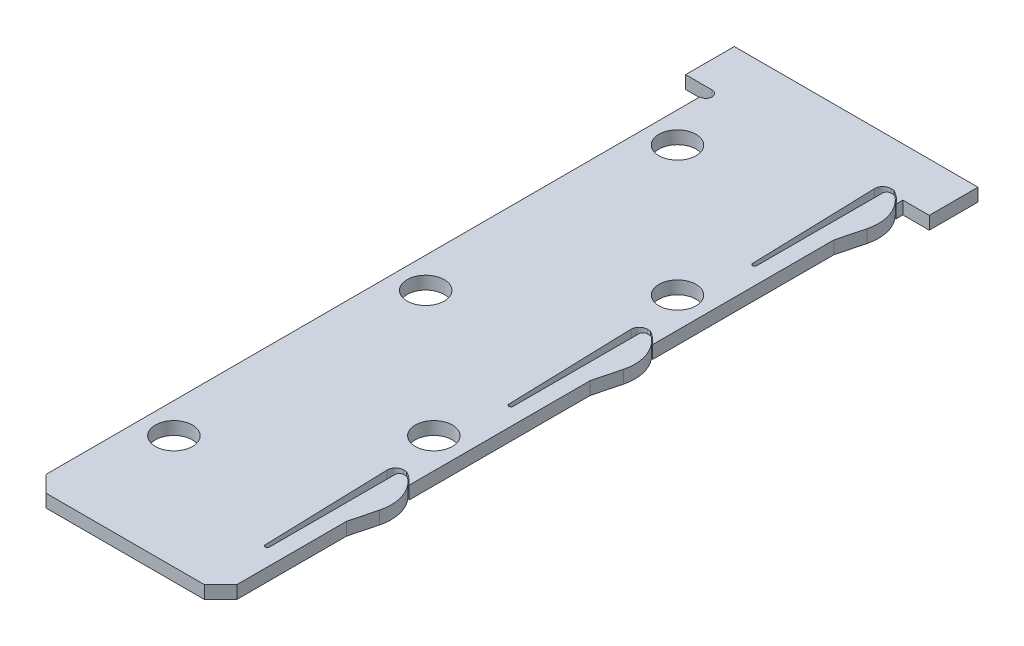
SolidWorks part; units mm, degrees
ref_plane "Front Plane" through (0, 0, 0) normal (0, 0, 1) x (1, 0, 0)
ref_plane "Top Plane" through (0, 0, 0) normal (0, 1, 0) x (1, 0, 0)
ref_plane "Right Plane" through (0, 0, 0) normal (1, 0, 0) x (0, 0, -1)
sketch "Sketch1" plane through (0, 0, 0) normal (0, 1, 0) x (1, 0, 0)
  line L0 (-11.75, -45) -> (11.75, 45) construction
  line L1 (-11.75, 45) -> (11.75, 45)
  line L2 (-11.75, 45) -> (-11.75, -45)
  line L3 (-11.75, -45) -> (11.75, -45)
  line L4 (11.75, 45) -> (11.75, -45)
  dimension "D1" = 23.5
  dimension "D2" = 90
extrude "Boss-Extrude1" add sketch "Sketch1" along normal blind 1.5875
sketch "Sketch2" plane through (0, 1.5875, 0) normal (0, 1, 0) x (1, 0, 0)
  line L0 (11.75, -45) -> (11.75, 45) construction
  line L1 (11.75, -29.5) -> (12.5905, -26.2529)
  line L2 (11.75, -29.5) -> (9.9294, -29.5)
  arc A0 (12.5905, -26.2529) -> (9.9294, -29.5) centre (7.75, -25) ccw
  dimension "D1" = 10
  dimension "D2" = 4
  dimension "D3" = 25
  dimension "D4" = 4.5
extrude "Boss-Extrude2" add sketch "Sketch2" against normal up to surface (1.5875 mm away) up to face at (0, 0, 0)
sketch "Sketch4" plane through (0, 1.5875, 0) normal (0, 1, 0) x (1, 0, 0)
  line L0 (10.75, -21) -> (9.75, -21)
  line L1 (9.75, -21) -> (9.75, -37)
  line L2 (9.2501, -37.0076) -> (8.75, -20.5)
  line L3 (8.75, -20.5) -> (10.15, -20.5)
  line L4 (11.75, -22) -> (11.75, 45) construction
  line L5 (11.75, -45) -> (11.75, -29.5) construction
  line L7 (11.75, -22) -> (11.75, -21.8361)
  arc A0 (11.75, -22) -> (10.75, -21) centre (7.75, -25) ccw
  arc A1 (12.5905, -26.2529) -> (11.75, -22) centre (7.75, -25) ccw construction
  arc A2 (10.15, -20.5) -> (11.75, -21.8361) centre (7.75, -25) cw
  arc A3 (9.75, -37) -> (9.2501, -37.0076) centre (9.5, -37) cw
  dimension "D3" = 0.25
  dimension "D4" = 0.1
  dimension "D1" = 4
  dimension "D2" = 2
  dimension "D5" = 12
  dimension "D6" = 0.5
  dimension "D7" = 1
extrude "Cut-Extrude3" cut sketch "Sketch4" against normal through all
pattern_linear "LPattern1" count 3 spacing 30 along (0, 0, -1) of "Cut-Extrude3", "Boss-Extrude2"
sketch "Sketch5" plane through (0, 1.5875, 0) normal (0, 1, 0) x (1, 0, 0)
  circle A0 centre (-8, -31) radius 2.286
  circle A1 centre (8, -15) radius 2.286
  circle A2 centre (-8, 31) radius 2.286
  circle A3 centre (8, 15) radius 2.286
  circle A4 centre (-8, 0) radius 2.286
  dimension "D1" = 4.572
  dimension "D2" = 31
  dimension "D3" = 8
  dimension "D4" = 31
  dimension "D5" = 15
  dimension "D6" = 8
  dimension "D7" = 15
extrude "Cut-Extrude4" cut sketch "Sketch5" against normal through all
chamfer "Chamfer1" distance 2 angle 45 2 edges at (-11.75, 0.7937, 45) (11.75, 0.7937, 45)
sketch "Sketch6" plane through (0, 1.5875, 0) normal (0, 1, 0) x (1, 0, 0)
  line L0 (11.75, 45) -> (-11.75, 45) construction
  line L1 (-15, 45) -> (-11.75, 45)
  line L2 (-15, 45) -> (-15, 39)
  line L3 (-15, 39) -> (-11.75, 39)
  line L4 (15, 45) -> (15, 39)
  line L7 (-11.75, 39) -> (-11.75, 45)
  line L8 (11.75, 45) -> (11.75, 39)
  line L9 (11.75, 38.1639) -> (11.75, 45) construction
  line L10 (11.75, 39) -> (15, 39)
  line L11 (11.75, 45) -> (15, 45)
  line L12 (-11.75, 45) -> (-11.75, -43) construction
  dimension "D1" = 30
  dimension "D2" = 39
extrude "Boss-Extrude3" add sketch "Sketch6" against normal up to surface (1.5875 mm away) up to face at (-8, 0, 2.286)
fillet "Fillet1" radius 1 3 edges at (8.75, 0.7937, 20.5) (8.75, 0.7937, -9.5) (8.75, 0.7937, -39.5)
fillet "Fillet2" radius 0.5 3 edges at (9.75, 0.7937, -39) (9.75, 0.7937, -9) (9.75, 0.7937, 21)
sketch "Sketch7" plane through (0, 1.5875, 0) normal (0, 1, 0) x (1, 0, 0)
  line L0 (-11.75, 39) -> (-11.75, -43) construction
  circle A0 centre (-11.75, 38.25) radius 0.75
  dimension "D1" = 1.5
extrude "Cut-Extrude5" cut sketch "Sketch7" against normal through all
